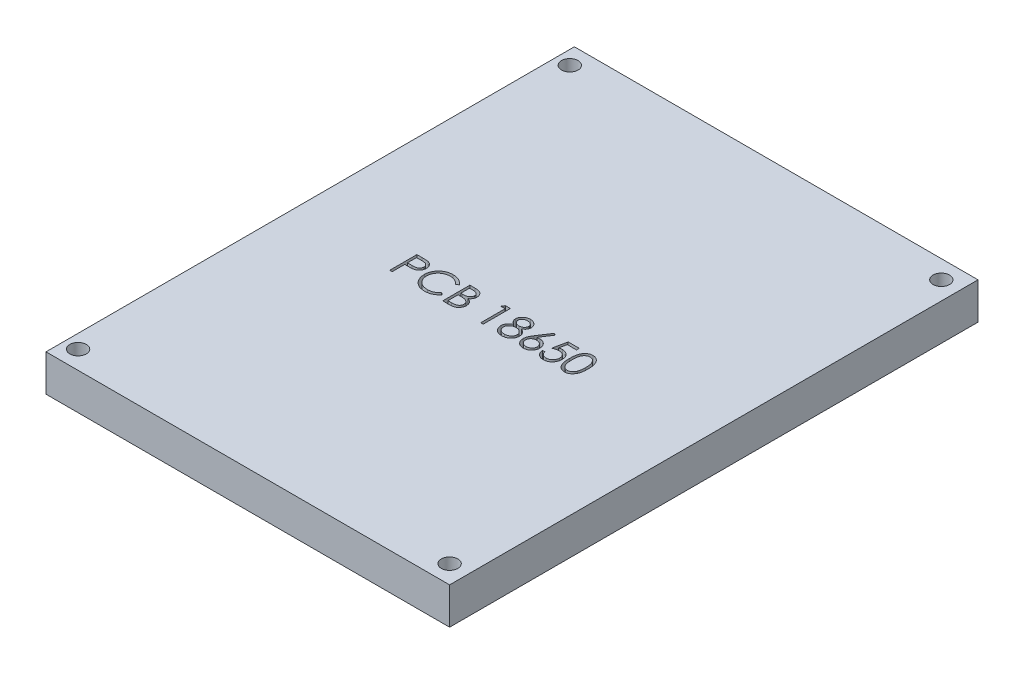
SolidWorks part; units mm, degrees
ref_plane "Alzado" through (0, 0, 0) normal (0, 0, 1) x (1, 0, 0)
ref_plane "Planta" through (0, 0, 0) normal (0, 1, 0) x (1, 0, 0)
ref_plane "Vista lateral" through (0, 0, 0) normal (1, 0, 0) x (0, 0, -1)
sketch "Croquis1" plane through (0, 0, 0) normal (0, 1, 0) x (1, 0, 0)
  line L1 (-63.912, 56.0185) -> (46.088, 56.0185)
  line L2 (-63.912, 56.0185) -> (-63.912, -87.9815)
  line L3 (-63.912, -87.9815) -> (46.088, -87.9815)
  line L4 (46.088, 56.0185) -> (46.088, -87.9815)
  dimension "D1" = 110
  dimension "D2" = 144
extrude "Saliente-Extruir1" add sketch "Croquis1" along normal blind 10
sketch "Croquis2" plane through (0, 10, 0) normal (0, 1, 0) x (1, 0, 0)
  text T0 "PCB 18650" font "Century Gothic" height in points 28
extrude "Cortar-Extruir1" cut sketch "Croquis2" against normal blind 3
sketch "Croquis3" plane through (0, 10, 0) normal (0, 1, 0) x (1, 0, 0)
  line L0 (46.088, 56.0185) -> (-63.912, 56.0185) construction
  line L3 (46.088, -87.9815) -> (46.088, 56.0185) construction
  line L4 (-63.912, 56.0185) -> (-63.912, -87.9815) construction
  line L6 (46.088, -15.9815) -> (-63.912, -15.9815) construction
  circle A0 centre (41.088, 51.0185) radius 2.25
  circle A1 centre (-60.162, 51.0185) radius 2.25
  circle A2 centre (-60.162, -82.9815) radius 2.25
  circle A3 centre (41.088, -82.9815) radius 2.25
  dimension "D1" = 4.5
  dimension "D4" = 4.5
  dimension "D5" = 5
  dimension "D6" = 3.75
  dimension "D2" = 5
  dimension "D3" = 5
extrude "Cortar-Extruir2" cut sketch "Croquis3" against normal blind 10
